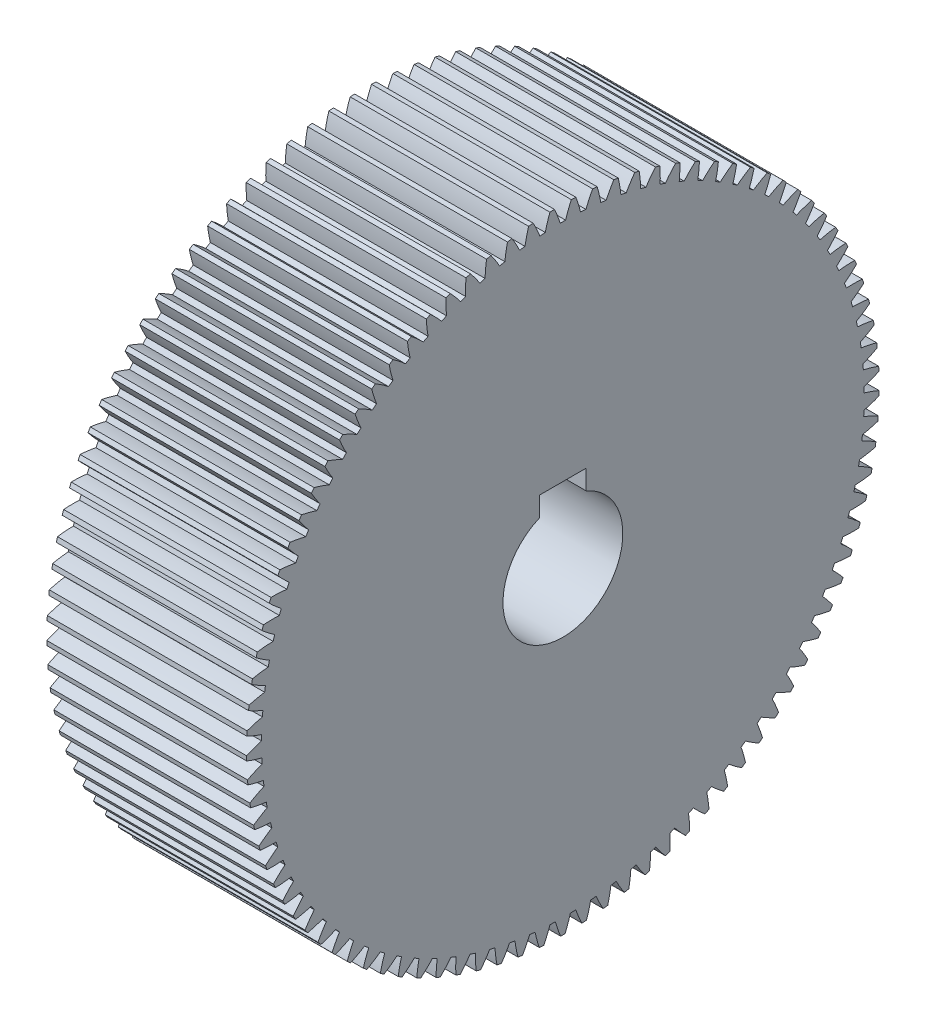
SolidWorks part; units mm, degrees
ref_plane "Plane1" through (0, 0, 0) normal (0, 0, 1) x (1, 0, 0)
ref_plane "Plane2" through (0, 0, 0) normal (0, 1, 0) x (1, 0, 0)
ref_plane "Plane3" through (0, 0, 0) normal (1, 0, 0) x (0, 0, -1)
sketch "HoldingSke" plane through (0, 0, 0) normal (0, 1, 0) x (1, 0, 0)
  line L0 (0, 0) -> (-0.0262, -0.4993)
  line L1 (-15, 0) -> (100, 0) construction
  line L2 (0, 0) -> (-2.1039, 2.3779)
  line L3 (0, 0) -> (-11.863, 4.5341)
  line L4 (0, 0) -> (-0.452, 8.6242)
  line L5 (0, 0) -> (-46.8476, -17.4728)
  line L6 (0, 0) -> (-49.7378, -33.5582)
  line L7 (-2.1039, 2.3779) -> (10.8111, 60.9715)
  line L8 (-76.2, 54.61) -> (-76.1, 54.61)
  line L9 (-71.009, 38.7566) -> (-53.1078, 45.2721)
  line L10 (-76.2, 71.12) -> (104.1128, 71.12)
  line L11 (0, 0) -> (-60, 0)
  line L12 (-76.2, 101.6) -> (-76.133, 101.6)
  line L13 (24.9733, 27.94) -> (52.9518, 28.4284)
  line L14 (24.9733, 27.94) -> (24.9743, 27.94)
  line L15 (24.9733, 27.94) -> (100.4006, 29.5858)
  line L16 (-63.627, -2) -> (-12.827, -2)
  circle A0 centre (0, 0) radius 0.4
  circle A1 centre (0, 0) radius 37.5
  circle A2 centre (0, 0) radius 37.5
  circle A3 centre (0, 0) radius 0.4
  dimension "MHD" = 75
  dimension "Hub_dia" = 75
  dimension "Bore" = 0.8
  dimension "MBD" = 0.8
  dimension "Num_teeth" = 93
  dimension "Pitch" = 0.5
  dimension "Overall_len" = 50
  dimension "Show_teeth" = 93
  dimension "Thickness" = 60
  dimension "OAL" = 60.0001
  dimension "T_dim" = 0.1
  dimension "Ap" = 20
  dimension "H" = 19.05
  dimension "Pitch_radius" = 180.3128
  dimension "Width" = 60
  dimension "Backlash" = 0.067
  dimension "Addendum_fac" = 1
  dimension "Dedendum_fac" = 1.25
  dimension "Clearance_fac" = 0.25
  dimension "Dedendum_add" = 0.001
  dimension "Module" = 2
sketch "BasProSke" plane through (0, 0, 0) normal (0, 1, 0) x (1, 0, 0)
  line L0 (-10, 0) -> (60, 0) construction
  line L1 (0, 0) -> (0, 95)
  line L2 (0, 0) -> (60, 0)
  line L3 (60, 0) -> (60, 95)
  line L4 (60, 95) -> (0, 95)
  dimension "Thickness" = 60
  dimension "Diameter" = 190
revolve "Base-Revolve" add sketch "BasProSke" angle 360 about L0
sketch "TooCutSke" plane through (0, 0, 0) normal (1, 0, 0) x (0, 0, -1)
  line L1 (0, 0) -> (0, 107) construction
  line L2 (0, 0) -> (-1.688, 92.9847) construction
  line L3 (0, 0) -> (-6.2812, 185.8712) construction
  line L4 (-1.688, 92.9847) -> (-3.1406, 92.9356) construction
  arc A0 (0.8179, 90.4953) -> (-0.8179, 90.4953) centre (0, 0) ccw
  arc A1 (2.5388, 94.9915) -> (-2.5388, 94.9915) centre (0, 0) ccw
  circle A2 centre (0, 0) radius 93 construction
  circle A3 centre (0, 0) radius 87.3914 construction
  arc A4 (-0.8179, 90.4953) -> (-2.5388, 94.9915) centre (-36.3477, 79.4739) ccw
  arc A5 (2.5388, 94.9915) -> (0.8179, 90.4953) centre (36.3477, 79.4739) ccw
  dimension "Root_dia" = 180.998
  dimension "Overcut_dia" = 190.0508
  dimension "Pitch_dia" = 186
  dimension "Base_dia" = 174.7828
  dimension "Flank_rad" = 37.2
  dimension "Half_ang" = 1.935
  dimension "Half_CT" = 1.4535
extrude "ToothCut" cut sketch "TooCutSke" along normal through all
fillet "Breaks" [suppressed] radius 0.04
fillet "RootFillets" [suppressed] radius 0.501
pattern_circular "TeethCuts" count 93 every 3.871 about axis through (-10, 0, 0) along (1, 0, 0) of "ToothCut", "RootFillets", "Breaks"
sketch "HubNeaOneSke" plane through (0, 0, 0) normal (-1, 0, 0) x (0, 0, 1)
  circle A0 centre (0, 0) radius 37.5
  dimension "Diameter" = 75
extrude "HubNearOne" [suppressed] add sketch "HubNeaOneSke" along normal blind 20.0001
sketch "HubNeaBotSke" plane through (0, 0, 0) normal (-1, 0, 0) x (0, 0, 1)
  circle A0 centre (0, 0) radius 37.5
  dimension "Diameter" = 75
extrude "HubNearBoth" [suppressed] add sketch "HubNeaBotSke" along normal blind 10
ref_plane "FarPln" through (60, 0, 0) normal (1, 0, 0) x (0, 0, -1)
sketch "HubFarSke" plane through (60, 0, 0) normal (1, 0, 0) x (0, 0, -1)
  circle A0 centre (0, 0) radius 37.5
  dimension "Diameter" = 75
extrude "HubFar" [suppressed] add sketch "HubFarSke" along normal blind 10
sketch "BorSke" plane through (0, 0, 0) normal (1, 0, 0) x (0, 0, -1)
  circle A0 centre (0, 0) radius 0.4
  dimension "Diameter" = 0.8
extrude "Bore" cut sketch "BorSke" along normal mid plane 120.0001
sketch "KeySke" plane through (0, 0, 0) normal (1, 0, 0) x (0, 0, -1)
  line L0 (-0.05, 0) -> (-0.05, 0.5)
  line L1 (-0.05, 0.5) -> (0.05, 0.5)
  line L2 (0.05, 0.5) -> (0.05, 0)
  line L3 (0, 0) -> (0, 34) construction
  line L4 (-0.05, 0) -> (0.05, 0)
  dimension "Offset" = 0.5
  dimension "Width" = 0.1
extrude "Keyway" [suppressed] cut sketch "KeySke" along normal mid plane 120.0001
pattern_circular "Keyway2" [suppressed] count 2 every 90 about axis through (-10, 0, 0) along (1, 0, 0)
sketch "Sketch1" plane through (60, 0, 0) normal (1, 0, 0) x (0, 0, -1)
  line L0 (0, 0.4) -> (0, 57.7817) construction
  line L2 (-7, 22.9) -> (7, 22.9)
  line L3 (-7, 22.9) -> (-7, 16.9831)
  line L5 (7, 22.9) -> (7, 16.9831)
  arc A0 (-7, 16.9831) -> (7, 16.9831) centre (0, 0.4) ccw
  circle A1 centre (0, 0) radius 0.4 construction
  dimension "D1" = 36
  dimension "D2" = 14
  dimension "D3" = 22.5
extrude "Cut-Extrude1" cut sketch "Sketch1" against normal through all contours A0 L5 L2 L3
equation "' \"Module@HoldingSke\" = 6.35"
equation "' \"Num_teeth@HoldingSke\" = 12"
equation "' \"Ap@HoldingSke\" =  20"
equation "' \"Ap@HoldingSke\" = 20"
equation "' \"Width@HoldingSke\" = 0.5 * 25.4"
equation "' \"Hub_dia@HoldingSke\"= 1 * 25.4"
equation "' \"Hub_dia@HoldingSke\" = 1 * 25.4"
equation "' \"Overall_len@HoldingSke\" = 1.0 * 25.4"
equation "' \"Bore@HoldingSke\" = 0.75 * 25.4"
equation "' \"T_dim@HoldingSke\" = 0.1 * 25.4"
equation "' \"Width@KeySke\" = 0.25 * 25.4"
equation "' \"Show_teeth@HoldingSke\" = 13"
equation "' \"Backlash@HoldingSke\" = 0.009 * 25.4"
equation "' \"Addendum_fac@HoldingSke\" = 1.0"
equation "' \"Dedendum_fac@HoldingSke\" = 1.25"
equation "' \"Dedendum_add@HoldingSke\" = 0.00005 * 25.4"
equation "' \"Clearance_fac@HoldingSke\" = 0.25"
equation "\"Pitch@HoldingSke\" = 1 / \"Module@HoldingSke\""
equation "\"Overcut_dia@TooCutSke\" = (\"Num_teeth@HoldingSke\" + 2 * \"Addendum_fac@HoldingSke\") / \"Pitch@HoldingSke\" + 0.002 * 25.4"
equation "\"Pitch_dia@TooCutSke\" = \"Num_teeth@HoldingSke\" / \"Pitch@HoldingSke\""
equation "\"Base_dia@TooCutSke\" = \"Num_teeth@HoldingSke\" / \"Pitch@HoldingSke\" * cos((\"Ap@HoldingSke\"  * 3.14159265 / 180))"
equation "\"Root_dia@TooCutSke\" = (\"Num_teeth@HoldingSke\" + 2) / \"Pitch@HoldingSke\" - 2 * (\"Addendum_fac@HoldingSke\" + \"Dedendum_fac@HoldingSke\") / \"Pitch@HoldingSke\" - \"Dedendum_add@HoldingSke\" * 2"
equation "\"Half_ang@TooCutSke\" = 180 / \"Num_teeth@HoldingSke\""
equation "\"Half_CT@TooCutSke\" = \"Num_teeth@HoldingSke\" / \"Pitch@HoldingSke\" * sin((3.14159265 / 2 / \"Num_teeth@HoldingSke\")) / 2 - 7 * \"Backlash@HoldingSke\" / 4"
equation "\"Flank_rad@TooCutSke\" = \"Num_teeth@HoldingSke\" / \"Pitch@HoldingSke\" / 5"
equation "\"Radius@RootFillets\" = \"Clearance_fac@HoldingSke\" / \"Pitch@HoldingSke\" + \"Dedendum_add@HoldingSke\""
equation "\"Break_rad@Breaks\" = 0.02 / \"Pitch@HoldingSke\""
equation "\"Thickness@HoldingSke\" = \"Width@HoldingSke\""
equation "\"OAL@HoldingSke\" = \"Thickness@HoldingSke\""
equation "\"MHD@HoldingSke\" = (\"Num_teeth@HoldingSke\" + 2) / \"Pitch@HoldingSke\" - 2 * (\"Addendum_fac@HoldingSke\" + \"Dedendum_fac@HoldingSke\")  / \"Pitch@HoldingSke\" - \"Dedendum_add@HoldingSke\" * 2"
equation "\"MBD@HoldingSke\" = (\"Num_teeth@HoldingSke\" + 2) / \"Pitch@HoldingSke\" - 2 * (\"Addendum_fac@HoldingSke\" + \"Dedendum_fac@HoldingSke\")  / \"Pitch@HoldingSke\" - \"Dedendum_add@HoldingSke\" * 2 - 0.002 * 25.4"
equation "\"MHD@HoldingSke\" = ((sgn( \"MHD@HoldingSke\" - \"Hub_dia@HoldingSke\" )-1)*( \"MHD@HoldingSke\" - \"Hub_dia@HoldingSke\" ))/-2+ \"Hub_dia@HoldingSke\""
equation "\"MBD@HoldingSke\" = ((sgn( \"MBD@HoldingSke\" - \"Bore@HoldingSke\" )-1)*( \"MBD@HoldingSke\" - \"Bore@HoldingSke\" ))/-2+ \"Bore@HoldingSke\""
equation "\"OAL@HoldingSke\" = ((sgn( \"OAL@HoldingSke\" - \"Overall_len@HoldingSke\" )+1)*( \"OAL@HoldingSke\" - \"Overall_len@HoldingSke\" ))/2 + \"Overall_len@HoldingSke\" + 0.000002 * 25.4"
equation "\"Num_teeth@TeethCuts\" = int( \"Show_teeth@HoldingSke\" ) + 1"
equation "\"Num_teeth@TeethCuts\" = ((sgn( \"Num_teeth@TeethCuts\" - \"Num_teeth@HoldingSke\" )-1)*( \"Num_teeth@TeethCuts\" - \"Num_teeth@HoldingSke\" ))/-2+ \"Num_teeth@HoldingSke\""
equation "\"Num_teeth@TeethCuts\" = ((sgn( \"Num_teeth@TeethCuts\" - 2.0)+1)*( \"Num_teeth@TeethCuts\" - 2.0))/2 +2.0"
equation "\"Angle@TeethCuts\" = 360.0 / \"Num_teeth@HoldingSke\""
equation "\"Diameter@BasProSke\" = (\"Num_teeth@HoldingSke\" + 2 * \"Addendum_fac@HoldingSke\") / \"Pitch@HoldingSke\""
equation "\"Thickness@BasProSke\"  = \"Thickness@HoldingSke\""
equation "' \"Fillet_rad@BasProSke\" =  \"Thickness@HoldingSke\" * 0.05"
equation "' \"Fillet_rad@BasProSke\" = \"Thickness@HoldingSke\" * 0.05"
equation "\"MHD@HoldingSke\" = ((sgn( \"MHD@HoldingSke\" - \"Root_dia@TooCutSke\" )-1)*( \"MHD@HoldingSke\" - \"Root_dia@TooCutSke\" ))/-2+ \"Root_dia@TooCutSke\""
equation "\"Diameter@HubNeaOneSke\" = \"MHD@HoldingSke\""
equation "\"Length@HubNearOne\" = \"OAL@HoldingSke\" - \"Thickness@BasProSke\""
equation "\"Diameter@HubNeaBotSke\" = \"MHD@HoldingSke\""
equation "\"Length@HubNearBoth\" = ( \"OAL@HoldingSke\" - \"Thickness@BasProSke\" ) / 2.0"
equation "\"Thickness@FarPln\" = \"Thickness@BasProSke\""
equation "\"Diameter@HubFarSke\" = \"MHD@HoldingSke\""
equation "\"Length@HubFar\" = ( \"OAL@HoldingSke\" - \"Thickness@BasProSke\" ) / 2.0"
equation "\"Diameter@BorSke\" = \"MBD@HoldingSke\""
equation "\"D1@Bore\" = \"OAL@HoldingSke\" * 2.0"
equation "\"D1@Keyway\" = \"OAL@HoldingSke\" * 2.0"
equation "\"Offset@KeySke\" = \"T_dim@HoldingSke\" + \"MBD@HoldingSke\" / 2.0"
